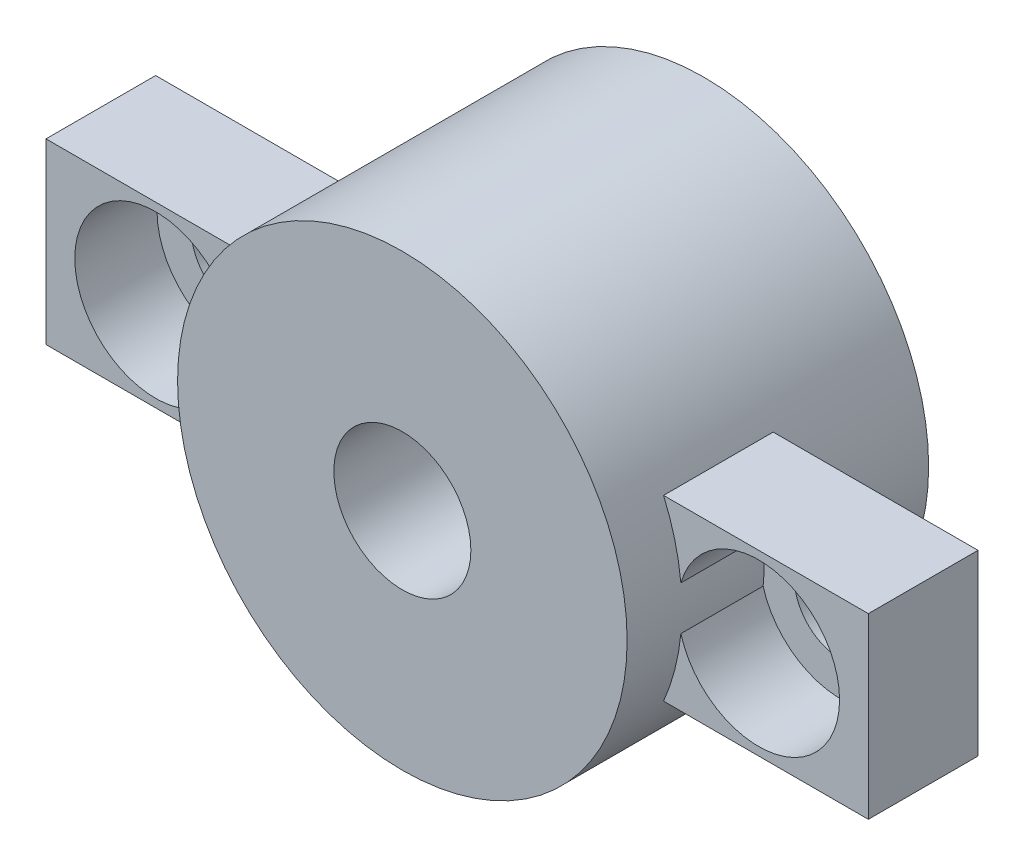
SolidWorks part; units mm, degrees
material "PLA"
ref_plane "Alzado" through (0, 0, 0) normal (0, 0, 1) x (1, 0, 0)
ref_plane "Planta" through (0, 0, 0) normal (0, 1, 0) x (1, 0, 0)
ref_plane "Vista lateral" through (0, 0, 0) normal (1, 0, 0) x (0, 0, -1)
sketch "Croquis1" plane through (0, 0, 0) normal (0, 0, 1) x (1, 0, 0)
  line L0 (-7.2005, 3.25) -> (-15, 3.25)
  line L1 (15, -3.25) -> (7.2005, -3.25)
  line L2 (15, -3.25) -> (15, 3.25)
  line L3 (15, 3.25) -> (7.2005, 3.25)
  line L4 (-15, -3.25) -> (-15, 3.25)
  line L5 (15, -3.25) -> (-15, 3.25) construction
  line L6 (15, 3.25) -> (-15, -3.25) construction
  line L9 (-7.2005, -3.25) -> (-15, -3.25)
  arc A0 (-7.2005, -3.25) -> (7.2005, -3.25) centre (0, 0) ccw
  circle A1 centre (0, 0) radius 2.5
  arc A2 (7.2005, 3.25) -> (-7.2005, 3.25) centre (0, 0) ccw
  dimension "D3" = 5
  dimension "D4" = 7.9
  dimension "D1" = 30
  dimension "D2" = 6.5
extrude "Saliente-Extruir1" add sketch "Croquis1" along normal blind 4
sketch "Croquis2" plane through (0, 0, 4) normal (0, 0, 1) x (1, 0, 0)
  line L0 (-11, 0) -> (11, 0) construction
  circle A0 centre (-11, 0) radius 1.7
  circle A1 centre (11, 0) radius 1.7
  point P2 (0, 0)
  dimension "D1" = 3.4
  dimension "D2" = 22
extrude "Cortar-Extruir1" cut sketch "Croquis2" against normal blind 4
sketch "Croquis3" plane through (0, 0, 4) normal (0, 0, 1) x (1, 0, 0)
  circle A0 centre (-11, 0) radius 2.95
  circle A1 centre (11, 0) radius 2.95
  dimension "D1" = 5.9
extrude "Cortar-Extruir2" cut sketch "Croquis3" against normal blind 3
sketch "Croquis4" plane through (0, 0, 4) normal (0, 0, 1) x (1, 0, 0)
  circle A2 centre (0, 0) radius 2.5 construction
  circle A3 centre (0, 0) radius 2.5
  circle A6 centre (0, 0) radius 8.2
  dimension "D1" = 16.4
extrude "Saliente-Extruir2" add sketch "Croquis4" along normal blind 2 and the other way blind 9
